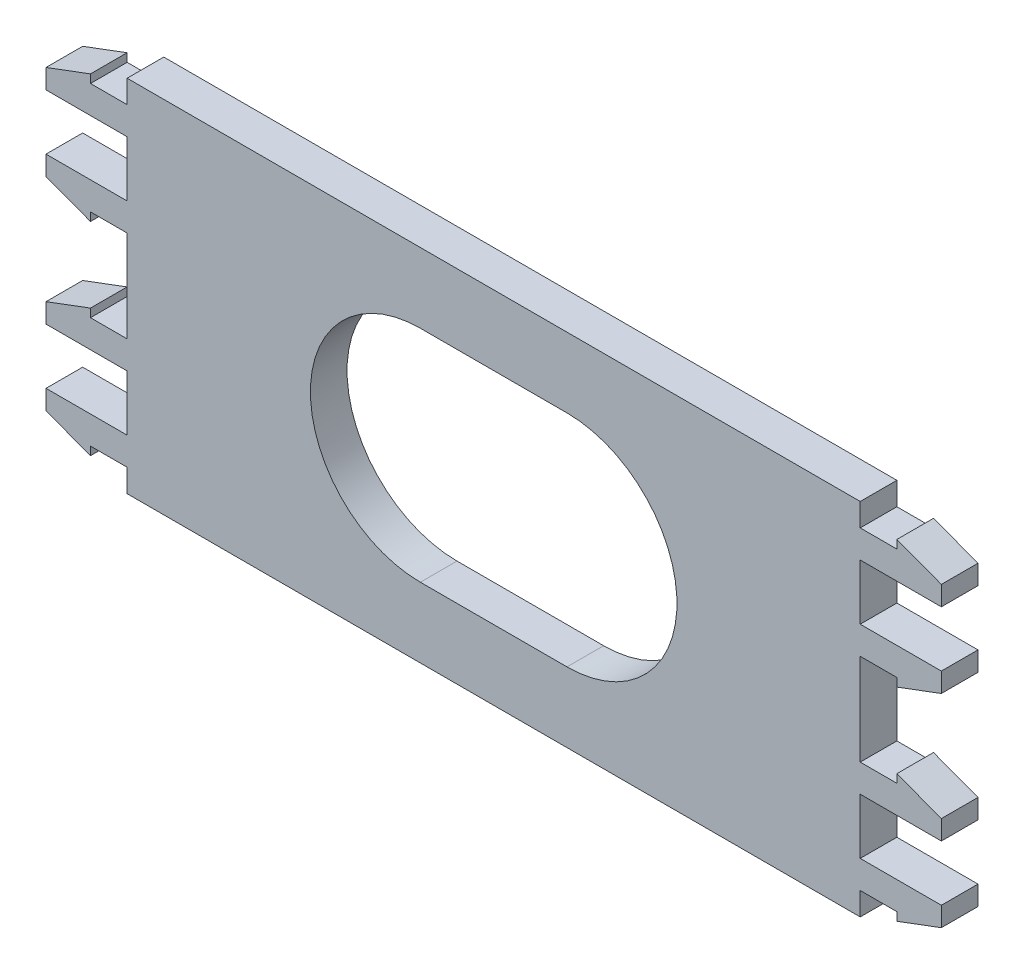
SolidWorks part; units mm, degrees
material "Pino"
ref_plane "Piano frontale" through (0, 0, 0) normal (0, 0, 1) x (1, 0, 0)
ref_plane "Piano superiore" through (0, 0, 0) normal (0, 1, 0) x (1, 0, 0)
ref_plane "Piano destro" through (0, 0, 0) normal (1, 0, 0) x (0, 0, -1)
sketch "Schizzo1" plane through (0, 0, 0) normal (0, 0, 1) x (1, 0, 0)
  line L0 (6, -115.594) -> (0, -115.594)
  line L1 (6, -100.594) -> (0, -100.594) construction
  line L2 (6, -100.594) -> (6, -82.394) construction
  line L3 (6, -82.394) -> (0, -82.394) construction
  line L4 (0, -115.594) -> (0, -133.794) construction
  line L5 (6, -100.594) -> (0, -100.594)
  line L6 (6, -100.594) -> (6, -82.394) construction
  line L7 (6, -82.394) -> (0, -82.394)
  line L8 (0, -115.594) -> (0, -133.794) construction
  line L9 (0, -100.594) -> (0, -115.594)
  line L10 (0, -82.394) -> (0, -78.644)
  line L11 (0, -78.644) -> (-120, -78.644)
  line L12 (-60, -78.644) -> (-60, -115.594) construction
  line L13 (-60, -115.594) -> (0, -115.594) construction
  line L14 (6, -82.394) -> (6, -81.029)
  line L15 (6, -81.029) -> (13.28, -83.759)
  line L16 (13.28, -83.759) -> (13.28, -86.944)
  line L17 (6, -91.494) -> (13.28, -91.494) construction
  line L18 (13.28, -86.944) -> (6, -86.944)
  line L19 (13.28, -86.944) -> (13.28, -91.494) construction
  line L20 (6, -86.944) -> (0, -86.944)
  line L21 (0, -86.944) -> (0, -96.044)
  line L22 (6, -100.594) -> (6, -101.959)
  line L23 (6, -101.959) -> (13.28, -99.229)
  line L24 (13.28, -99.229) -> (13.28, -96.044)
  line L25 (13.28, -96.044) -> (6, -96.044)
  line L26 (6, -96.044) -> (0, -96.044)
  line L27 (0, -108.094) -> (-60, -108.094) construction
  line L28 (-72, -90.094) -> (-48, -90.094)
  line L29 (6, -115.594) -> (6, -114.229)
  line L30 (6, -114.229) -> (13.28, -116.959)
  line L31 (13.28, -116.959) -> (13.28, -120.144)
  line L32 (13.28, -120.144) -> (6, -120.144)
  line L33 (6, -120.144) -> (0, -120.144)
  line L34 (0, -129.244) -> (0, -120.144)
  line L35 (6, -129.244) -> (0, -129.244)
  line L36 (13.28, -129.244) -> (6, -129.244)
  line L37 (13.28, -132.429) -> (13.28, -129.244)
  line L38 (6, -135.159) -> (13.28, -132.429)
  line L39 (6, -133.794) -> (6, -135.159)
  line L40 (6, -133.794) -> (0, -133.794)
  line L41 (0, -133.794) -> (0, -137.544)
  line L42 (0, -137.544) -> (-120, -137.544)
  line L43 (-72, -126.094) -> (-48, -126.094)
  line L44 (-120, -133.794) -> (-120, -137.544)
  line L45 (-126, -133.794) -> (-120, -133.794)
  line L46 (-126, -133.794) -> (-126, -135.159)
  line L47 (-126, -135.159) -> (-133.28, -132.429)
  line L48 (-133.28, -132.429) -> (-133.28, -129.244)
  line L49 (-133.28, -129.244) -> (-126, -129.244)
  line L50 (-126, -129.244) -> (-120, -129.244)
  line L51 (-120, -129.244) -> (-120, -120.144)
  line L52 (-126, -120.144) -> (-120, -120.144)
  line L53 (-133.28, -120.144) -> (-126, -120.144)
  line L54 (-133.28, -116.959) -> (-133.28, -120.144)
  line L55 (-126, -114.229) -> (-133.28, -116.959)
  line L56 (-126, -115.594) -> (-126, -114.229)
  line L57 (-126, -115.594) -> (-120, -115.594)
  line L58 (-120, -100.594) -> (-120, -115.594)
  line L59 (-126, -100.594) -> (-120, -100.594)
  line L60 (-126, -100.594) -> (-126, -101.959)
  line L61 (-126, -101.959) -> (-133.28, -99.229)
  line L62 (-133.28, -99.229) -> (-133.28, -96.044)
  line L63 (-133.28, -96.044) -> (-126, -96.044)
  line L64 (-126, -96.044) -> (-120, -96.044)
  line L65 (-120, -86.944) -> (-120, -96.044)
  line L66 (-126, -86.944) -> (-120, -86.944)
  line L67 (-133.28, -86.944) -> (-126, -86.944)
  line L68 (-133.28, -83.759) -> (-133.28, -86.944)
  line L69 (-126, -81.029) -> (-133.28, -83.759)
  line L70 (-126, -82.394) -> (-126, -81.029)
  line L71 (-126, -82.394) -> (-120, -82.394)
  line L72 (-120, -82.394) -> (-120, -78.644)
  arc A0 (-48, -90.094) -> (-48, -126.094) centre (-48, -108.094) cw
  arc A1 (-72, -90.094) -> (-72, -126.094) centre (-72, -108.094) ccw
  point P23 (0, -91.494)
  point P45 (-30, -108.094)
  point P47 (-60, -90.094)
  point P49 (-60, -126.094)
  point P50 (-60, -137.544)
extrude "Estrusione-Estrusione1" add sketch "Schizzo1" along normal blind 6
equation "\"D1@Schizzo1\"=(( \"material_thickness@spool_holder.Assembly\" *3)+( \"kerf@spool_holder.Assembly\" *2))*0.075"
equation "\"D2@Schizzo1\"=(( \"material_thickness@spool_holder.Assembly\" *3)+( \"kerf@spool_holder.Assembly\" *2))*0.25"
equation "\"D3@Schizzo1\"=(( \"material_thickness@spool_holder.Assembly\" *3)+( \"kerf@spool_holder.Assembly\" *2))*0.4"
equation "\"D4@Schizzo1\"=(( \"material_thickness@spool_holder.Assembly\" *3)+( \"kerf@spool_holder.Assembly\" *2))*0.075"
equation "\"D5@Schizzo1\"=(\"material_thickness@spool_holder.Assembly\" * 2.5) * 0.25"
equation "\"D6@Schizzo1\"=( \"spool_width@spool_holder.Assembly\" )/2"
equation "\"D8@Schizzo1\"=( \"spool_width@spool_holder.Assembly\" )*0.15"
equation "\"D7@Schizzo1\"=( \"spool_width@spool_holder.Assembly\" )*0.25"
equation "\"D1@Estrusione-Estrusione1\"=\"material_thickness@spool_holder.Assembly\" "
